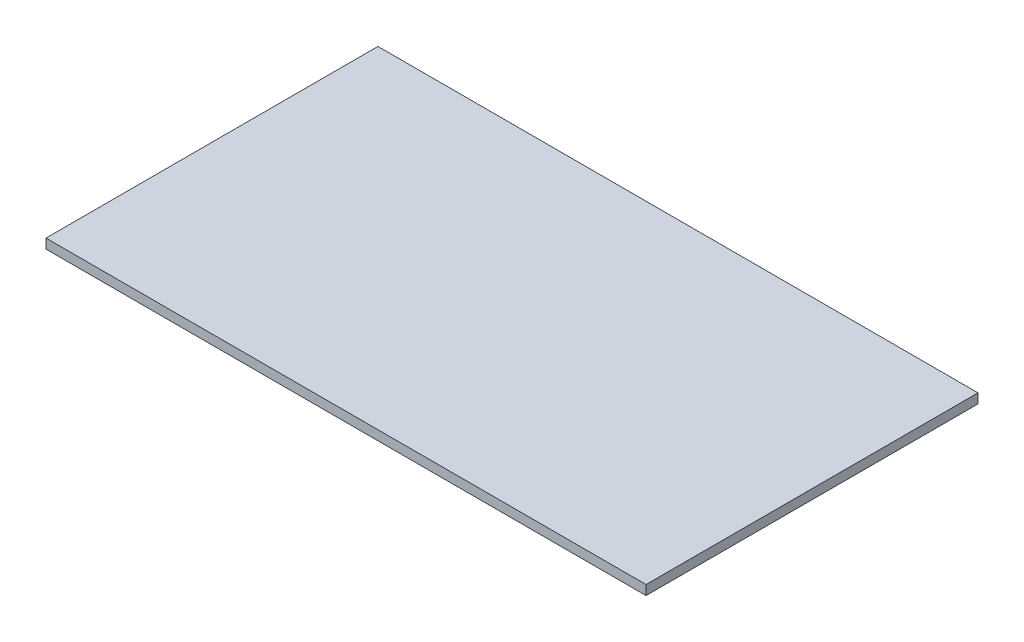
SolidWorks part; units mm, degrees
ref_plane "Front Plane" through (0, 0, 0) normal (0, 0, 1) x (1, 0, 0)
ref_plane "Top Plane" through (0, 0, 0) normal (0, 1, 0) x (1, 0, 0)
ref_plane "Right Plane" through (0, 0, 0) normal (1, 0, 0) x (0, 0, -1)
sketch "Sketch1" plane through (0, 0, 0) normal (0, 1, 0) x (1, 0, 0)
  line L1 (0, 0) -> (298.45, 0)
  line L2 (0, 0) -> (0, -165.1)
  line L3 (0, -165.1) -> (298.45, -165.1)
  line L4 (298.45, 0) -> (298.45, -165.1)
  dimension "D1" = 165.1
  dimension "D2" = 298.45
extrude "Boss-Extrude1" add sketch "Sketch1" along normal blind 4.7625 contours L1 L4 L3 L2
